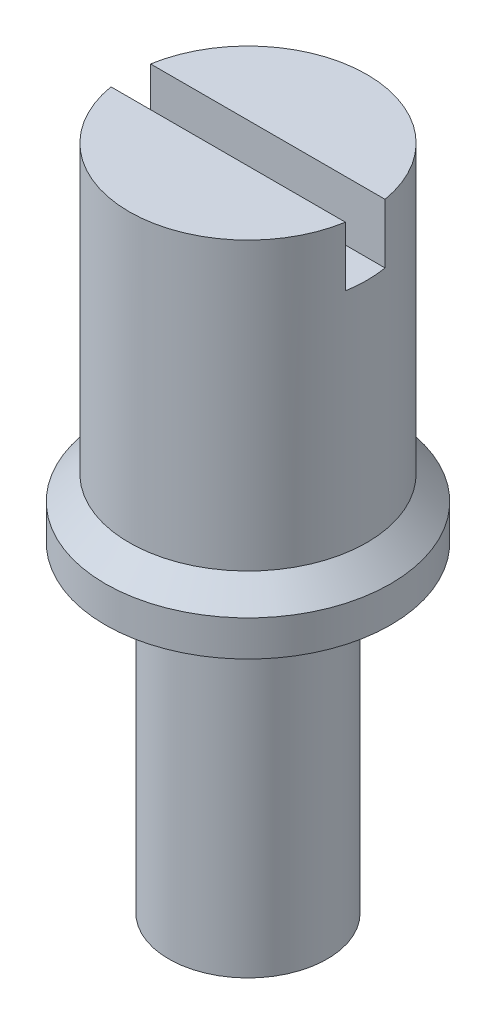
SolidWorks part; units mm, degrees
ref_plane "Front" through (0, 0, 0) normal (0, 0, 1) x (1, 0, 0)
ref_plane "Top" through (0, 0, 0) normal (0, 1, 0) x (1, 0, 0)
ref_plane "Right" through (0, 0, 0) normal (1, 0, 0) x (0, 0, -1)
sketch "Sketch2" plane through (0, 0, 0) normal (0, 0, 1) x (1, 0, 0)
  line L0 (0, 43.3234) -> (0, -43.3234) construction
  line L1 (0, -8.1) -> (2, -8.1)
  line L2 (2, -8.1) -> (2, 0)
  line L3 (2, 0) -> (3.6, 0)
  line L4 (3.6, 0) -> (3.6, 0.9)
  line L5 (3.6, 0.9) -> (3, 1.5)
  line L6 (3, 1.5) -> (3, 8.7312)
  line L7 (3, 8.7312) -> (0, 8.7312)
  line L8 (0, 8.7312) -> (0, -8.1)
  dimension "D1" = 4
  dimension "D2" = 6
  dimension "D3" = 7.2
  dimension "D4" = 8.1
  dimension "D5" = 0.9
  dimension "D6" = 0.6
  dimension "D7" = 8.7312
revolve "Revolve1" add sketch "Sketch2" angle 360 about L0
sketch "Sketch3" plane through (0, 8.7312, 0) normal (0, 1, 0) x (1, 0, 0)
  line L1 (-3, -0.5) -> (3, -0.5)
  line L2 (-3, -0.5) -> (-3, 0.5)
  line L3 (-3, 0.5) -> (3, 0.5)
  line L4 (3, -0.5) -> (3, 0.5)
  line L5 (-3, -0.5) -> (3, 0.5) construction
  line L6 (-3, 0.5) -> (3, -0.5) construction
  circle A0 centre (0, 0) radius 3 construction
  point P0 (0, 0)
  dimension "D1" = 1
extrude "Cut-Extrude1" cut sketch "Sketch3" against normal blind 1.5 contours L3 L4 L1 L2
